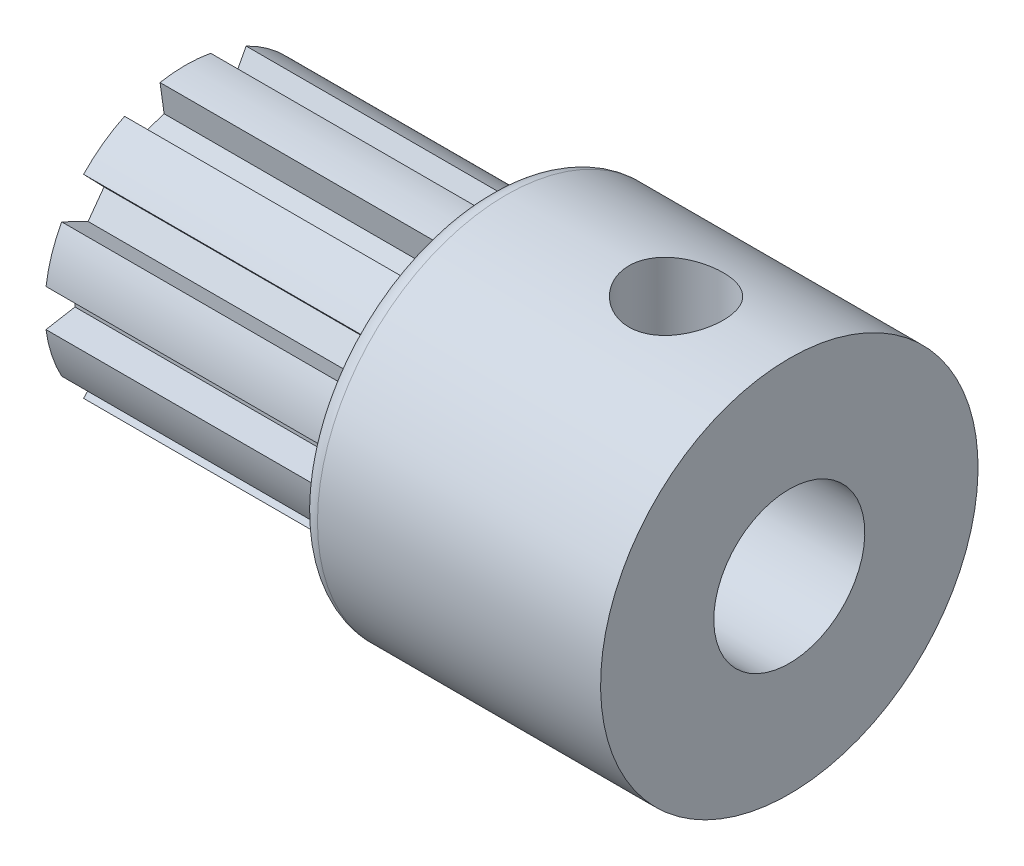
SolidWorks part; units mm, degrees
material "3.1325 (EN-AW 2017A)"
ref_plane "Plan de face" through (0, 0, 0) normal (0, 0, 1) x (1, 0, 0)
ref_plane "Plan de dessus" through (0, 0, 0) normal (0, 1, 0) x (1, 0, 0)
ref_plane "Plan de droite" through (0, 0, 0) normal (1, 0, 0) x (0, 0, -1)
sketch "Esquisse1" plane through (0, 0, 0) normal (0, 0, 1) x (1, 0, 0)
  line L0 (0, 0) -> (0, 3.725)
  line L1 (0, 3.725) -> (8, 3.725)
  line L2 (8, 3.725) -> (8, 5)
  line L3 (8, 5) -> (16, 5)
  line L4 (16, 5) -> (16, 0)
  line L5 (16, 0) -> (0, 0)
  dimension "D1" = 5
  dimension "D2" = 3.725
  dimension "D3" = 8
  dimension "D4" = 16
revolve "Révolution1" add sketch "Esquisse1" angle 360 about L5
sketch "Esquisse2" plane through (16, 0, 0) normal (1, 0, 0) x (0, 0, -1)
  circle A0 centre (0, 0) radius 2
extrude "Enlèv. mat.-Extru.1" cut sketch "Esquisse2" against normal through all
fillet "Congé1" radius 0.5 1 edges at (8, 5, 0)
sketch "Esquisse3" plane through (0, 0, 0) normal (-1, 0, 0) x (0, 0, 1)
  line L0 (0.6756, 3.6972) -> (0.5625, 2.8928)
  line L4 (0.6756, 3.6972) -> (1.6266, 3.3882)
  line L5 (0.5625, 2.8928) -> (1.2452, 2.6709)
  line L7 (1.6266, 3.3882) -> (1.2452, 2.6709)
extrude "Enlèv. mat.-Extru.2" cut sketch "Esquisse3" against normal blind 8
pattern_circular "Répétition circulaire1" count 10 over 360 about axis through (0, 0, 0) along (1, 0, 0) of "Enlèv. mat.-Extru.2"
hole_wizard "Trou taraudé M31" positions "Esquisse5" profile "Esquisse4" tap size "M3" standard "ISO"
sketch "Esquisse5" plane through (0, 0, 0) normal (0, 1, 0) x (1, 0, 0)
  line L0 (16, -5) -> (16, 5) construction
  point P0 (13, 0)
  dimension "D1" = 3
sketch "Esquisse4" plane through (13, 0, 0) normal (1, 0, 0) x (0, 0, -1)
  line L0 (0, 0) -> (0, 5)
  line L1 (0, 5) -> (1.25, 5)
  line L2 (1.25, 5) -> (1.25, 0)
  line L5 (1.25, 0) -> (0, 0)
  line L11 (0, -6.35) -> (0, 107.95) construction
  dimension "Diamètre du trou pour taraudage jusqu'au prochain" = 2.5
  dimension "Profondeur du trou pour taraudage jusqu'au prochain" = 5
cosmetic thread "Filetage de perçage1" parameters "D2"=3
